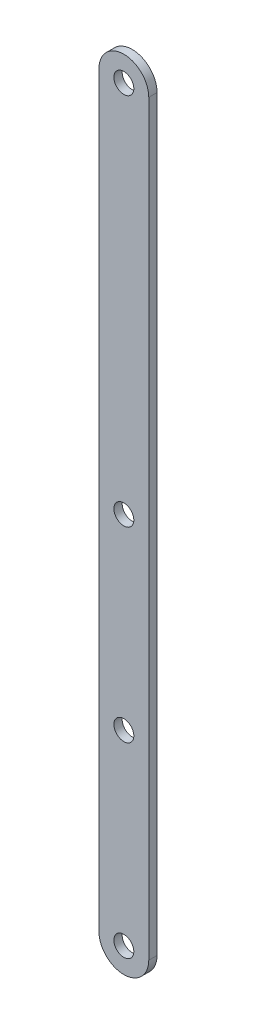
SolidWorks part; units mm, degrees
ref_plane "前视基准面" through (0, 0, 0) normal (0, 0, 1) x (1, 0, 0)
ref_plane "上视基准面" through (0, 0, 0) normal (0, 1, 0) x (1, 0, 0)
ref_plane "右视基准面" through (0, 0, 0) normal (1, 0, 0) x (0, 0, -1)
sketch "草图1" plane through (0, 0, 0) normal (0, 0, 1) x (1, 0, 0)
  line L1 (8.3631, 62.6958) -> (8.3631, 512.6958)
  line L3 (38.3631, 512.6958) -> (38.3631, 62.6958)
  line L4 (38.3631, 62.6958) -> (8.3631, 62.6958) construction
  line L6 (23.3631, 512.6958) -> (23.3631, 62.6958) construction
  line L7 (23.3631, 512.6958) -> (23.3631, 287.6958) construction
  line L8 (8.3631, 287.6958) -> (38.3631, 287.6958) construction
  circle A0 centre (23.3631, 512.6958) radius 6
  arc A1 (38.3631, 512.6958) -> (8.3631, 512.6958) centre (23.3631, 512.6958) ccw
  circle A2 centre (23.3631, 62.6958) radius 6
  arc A4 (8.3631, 62.6958) -> (38.3631, 62.6958) centre (23.3631, 62.6958) ccw
  circle A5 centre (23.3631, 287.6958) radius 6
  circle A7 centre (23.3631, 175.1958) radius 6
  dimension "D2" = 450
  dimension "D4" = 12
  dimension "D5" = 12
  dimension "D1" = 12
  dimension "D3" = 30
extrude "凸台-拉伸1" add sketch "草图1" along normal blind 5
